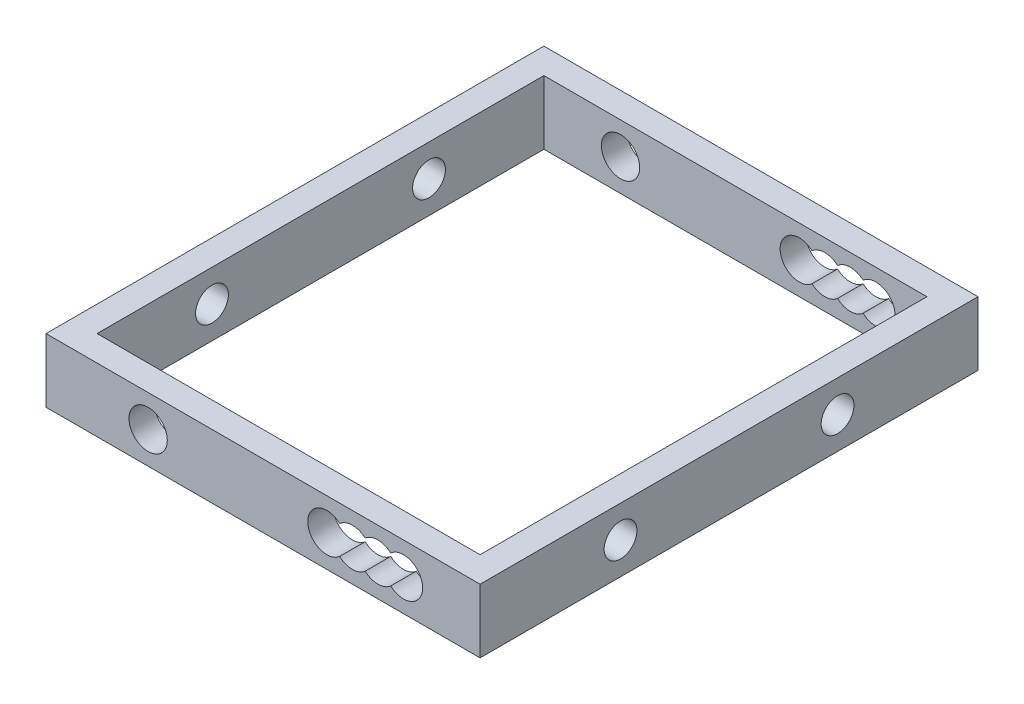
SolidWorks part; units mm, degrees
material "Náilon 6/10"
ref_plane "Plano frontal" through (0, 0, 0) normal (0, 0, 1) x (1, 0, 0)
ref_plane "Plano superior" through (0, 0, 0) normal (0, 1, 0) x (1, 0, 0)
ref_plane "Plano direito" through (0, 0, 0) normal (1, 0, 0) x (0, 0, -1)
sketch "Esboço1" plane through (0, 0, 0) normal (0, 0, 1) x (1, 0, 0)
  line L0 (6.1025, -1.0171) -> (15, -2.5) construction
  line L1 (-15, -2.5) -> (15, -2.5)
  line L2 (-15, -2.5) -> (-15, 2.5)
  line L3 (-15, 2.5) -> (15, 2.5)
  line L4 (15, -2.5) -> (15, 2.5)
  line L5 (-15, -2.5) -> (15, 2.5) construction
  line L6 (-15, 2.5) -> (3.6272, -0.6045) construction
  circle A0 centre (-9, 0) radius 1.5
  arc A1 (6, 1.118) -> (6, -1.118) centre (5, 0) ccw
  arc A2 (8, 1.118) -> (6, 1.118) centre (7, 0) ccw
  arc A3 (8, -1.118) -> (10, -1.118) centre (9, 0) ccw
  arc A4 (6, -1.118) -> (8, -1.118) centre (7, 0) ccw
  arc A5 (10, -1.118) -> (10, 1.118) centre (11, 0) ccw
  arc A6 (10, 1.118) -> (8, 1.118) centre (9, 0) ccw
  point P0 (0, 0)
  dimension "D3" = 3
  dimension "D1" = 30
  dimension "D2" = 5
  dimension "D4" = 6
  dimension "D5" = 14
  dimension "D6" = 16
  dimension "D7" = 18
  dimension "D8" = 20
extrude "Ressalto-extrusão1" add sketch "Esboço1" along normal blind 2
sketch "Esboço3" plane through (0, 0, 2) normal (0, 0, 1) x (1, 0, 0)
  line L1 (15, -2.5) -> (17, -2.5)
  line L2 (15, -2.5) -> (15, 2.5)
  line L3 (15, 2.5) -> (17, 2.5)
  line L4 (17, -2.5) -> (17, 2.5)
  dimension "D1" = 2
extrude "Ressalto-extrusão2" add sketch "Esboço3" against normal blind 39
pattern_linear "Padrão linear1" count 2 spacing 37 along (0, 0, -1) of "Ressalto-extrusão1"
mirror "Espelhar1" about plane through (0, 0, 0) normal (1, 0, 0) of "Ressalto-extrusão2"
sketch "Esboço4" plane through (17, 0, 0) normal (1, 0, 0) x (0, 0, -1)
  line L0 (37, -2.5) -> (37, 2.5) construction
  circle A0 centre (9, 0) radius 1.2853
  circle A1 centre (26, 0) radius 1.2853
  dimension "D1" = 17
  dimension "D2" = 11
extrude "Corte-extrusão1" cut sketch "Esboço4" against normal blind 39
